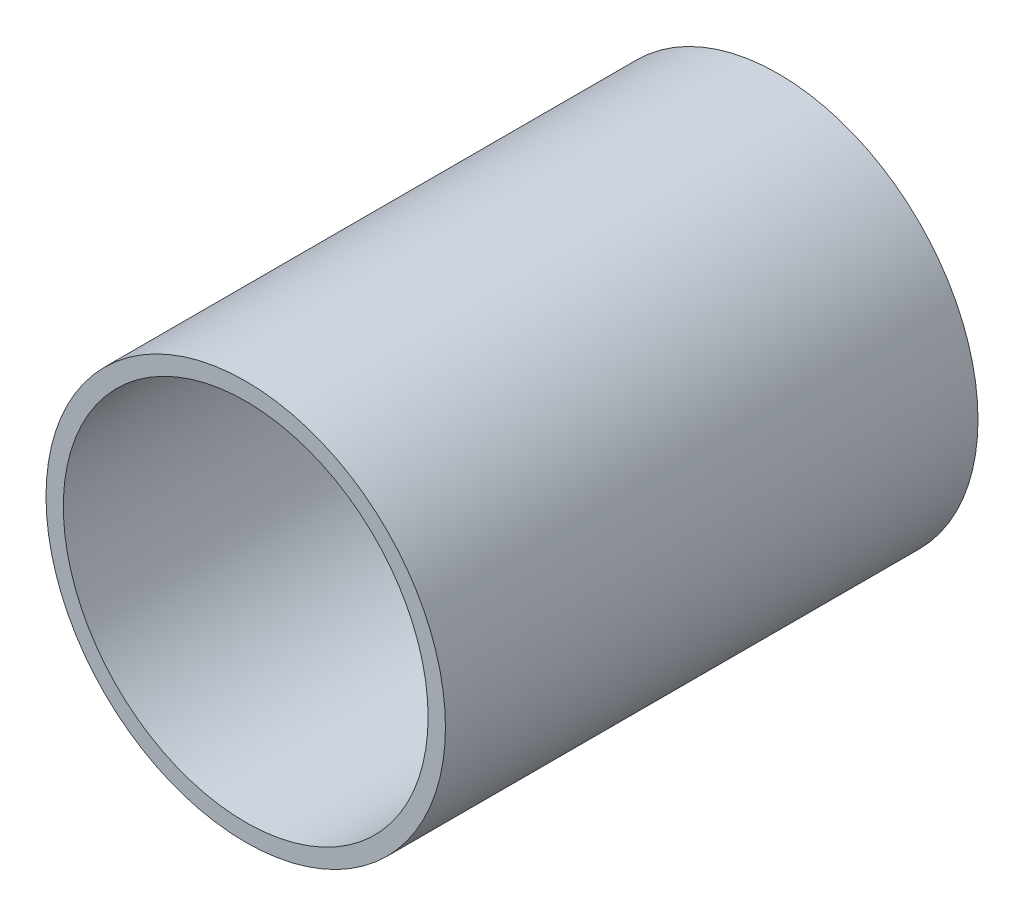
SolidWorks part; units mm, degrees
ref_plane "Front Plane" through (0, 0, 0) normal (0, 0, 1) x (1, 0, 0)
ref_plane "Top Plane" through (0, 0, 0) normal (0, 1, 0) x (1, 0, 0)
ref_plane "Right Plane" through (0, 0, 0) normal (1, 0, 0) x (0, 0, -1)
sketch "Sketch1" plane through (0, 0, 0) normal (0, 0, 1) x (1, 0, 0)
  circle A0 centre (0, 0) radius 19.05
  circle A1 centre (0, 0) radius 17.399
  dimension "D1" = 1.651
  dimension "D2" = 38.1
extrude "Extrude1" add sketch "Sketch1" along normal blind 50.8
